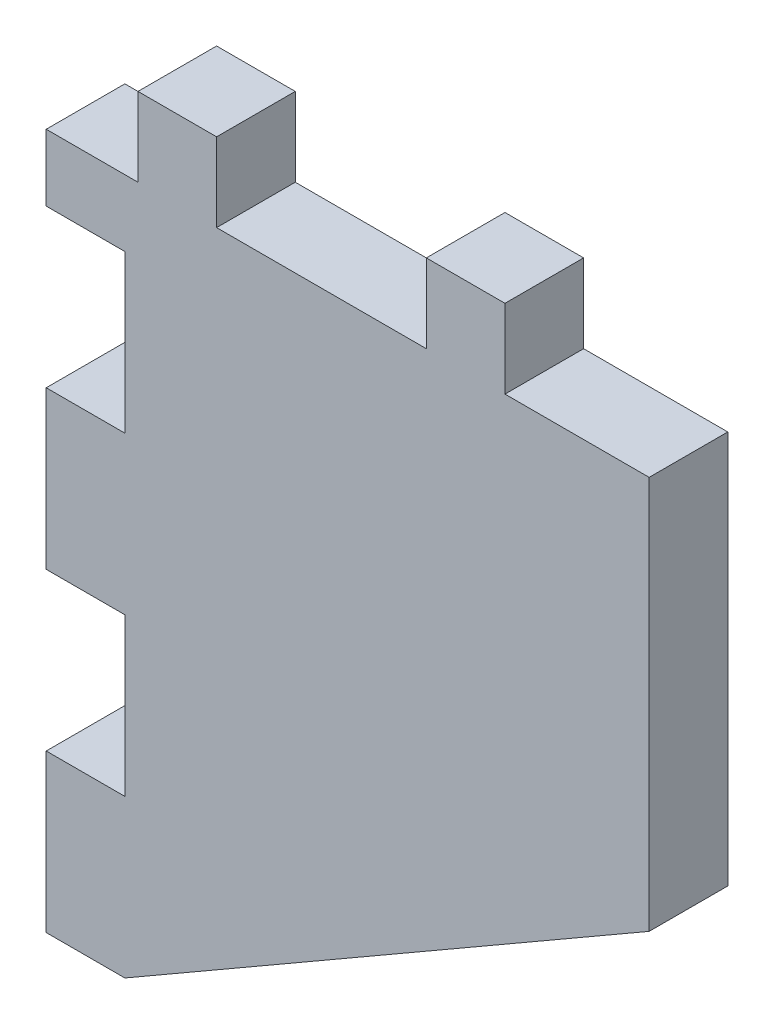
SolidWorks part; units mm, degrees
ref_plane "Front Plane" through (0, 0, 0) normal (0, 0, 1) x (1, 0, 0)
ref_plane "Top Plane" through (0, 0, 0) normal (0, 1, 0) x (1, 0, 0)
ref_plane "Right Plane" through (0, 0, 0) normal (1, 0, 0) x (0, 0, -1)
sketch "Sketch1" plane through (0, 0, 0) normal (0, 0, 1) x (1, 0, 0)
  line L0 (-131.298, 0) -> (131.298, 0) construction
  line L1 (0, 101.0044) -> (0, -102.5619) construction
  line L2 (-0.1266, 14.9296) -> (-0.1266, -0.0704)
  line L6 (-3.1266, 14.9296) -> (-11.1266, 14.9296)
  line L10 (-14.1266, 14.9296) -> (-23.1266, 14.9296)
  line L11 (-23.1266, 14.9296) -> (-23.1266, 12.3896)
  line L12 (-23.1266, 12.3896) -> (-20.1266, 12.3896)
  line L13 (-20.1266, 12.3896) -> (-20.1266, 6.3896)
  line L14 (-20.1266, 6.3896) -> (-23.1266, 6.3896)
  line L15 (-23.1266, 6.3896) -> (-23.1266, 0.3896)
  line L16 (-23.1266, 0.3896) -> (-20.1266, 0.3896)
  line L17 (-20.1266, 0.3896) -> (-20.1266, -5.6104)
  line L18 (-20.1266, -5.6104) -> (-23.1266, -5.6104)
  line L19 (-23.1266, -5.6104) -> (-23.1266, -11.6104)
  line L20 (-23.1266, -11.6104) -> (-20.1266, -11.6104)
  line L21 (-20.1266, -11.6104) -> (-0.1266, -0.0704)
  line L22 (-14.1266, 14.9296) -> (-11.1266, 14.9296)
  line L23 (-3.1266, 14.9296) -> (-0.1266, 14.9296)
extrude "Boss-Extrude1" add sketch "Sketch1" along normal blind 3
sketch "Sketch2" plane through (0, 0, 3) normal (0, 0, 1) x (1, 0, 0)
  line L1 (-0.1266, 14.9296) -> (-23.1266, 14.9296) construction
  line L3 (-0.1266, -0.0704) -> (-0.1266, 14.9296) construction
  line L4 (-5.6266, 14.9296) -> (-8.6266, 14.9296)
  line L5 (-5.6266, 14.9296) -> (-5.6266, 17.9296)
  line L6 (-5.6266, 17.9296) -> (-8.6266, 17.9296)
  line L7 (-8.6266, 14.9296) -> (-8.6266, 17.9296)
  line L8 (-16.6266, 14.9296) -> (-19.6266, 14.9296)
  line L9 (-16.6266, 14.9296) -> (-16.6266, 17.9296)
  line L10 (-16.6266, 17.9296) -> (-19.6266, 17.9296)
  line L11 (-19.6266, 14.9296) -> (-19.6266, 17.9296)
  point P13 (-18.1266, 17.9296)
  dimension "D1" = 3
  dimension "D2" = 3
  dimension "D3" = 8
  dimension "D4" = 5.5
  dimension "D5" = 3
  dimension "D6" = 3
extrude "Boss-Extrude2" add sketch "Sketch2" against normal blind 3
